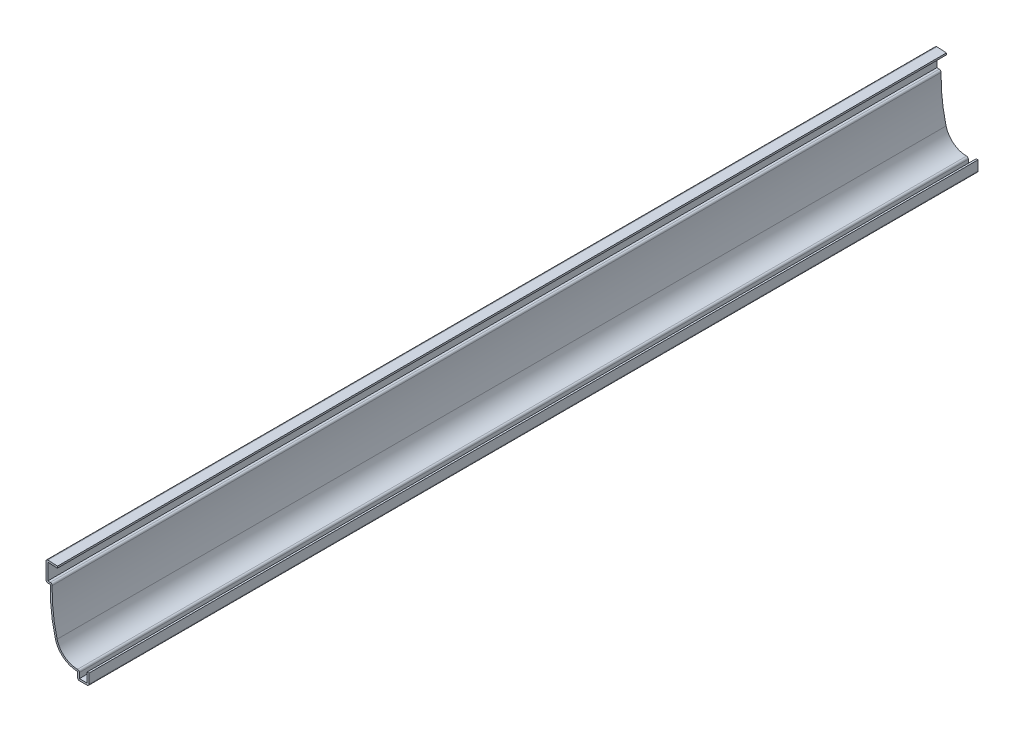
SolidWorks part; units mm, degrees
ref_plane "Front Plane" through (0, 0, 0) normal (0, 0, 1) x (1, 0, 0)
ref_plane "Top Plane" through (0, 0, 0) normal (0, 1, 0) x (1, 0, 0)
ref_plane "Right Plane" through (0, 0, 0) normal (1, 0, 0) x (0, 0, -1)
sketch "Sketch1" plane through (0, 0, 0) normal (0, 0, 1) x (1, 0, 0)
  line L0 (0, 6.35) -> (0, 0)
  line L1 (0, 0) -> (-6.35, 0)
  line L2 (-6.35, 0) -> (-6.35, 3.9687)
  line L3 (-21.4313, 38.1) -> (-23.8125, 38.1)
  line L4 (-23.8125, 38.1) -> (-23.8125, 49.2125)
  line L5 (-23.8125, 49.2125) -> (-17.4625, 48.8797)
  arc A0 (-6.35, 3.9687) -> (-18.6477, 13.4976) centre (-6.35, 16.6688) cw
  arc A1 (-18.6477, 13.4976) -> (-21.4313, 38.1) centre (67.4362, 35.6959) cw
  point P9 (49.8498, 29.128)
  point P13 (-17.7266, 28.566)
  point P14 (-21.6126, 38.1)
  dimension "D3" = 12.7
  dimension "D5" = 88.9
  dimension "D6" = 34.1313
  dimension "D12" = 2.3813
  dimension "D1" = 6.35
  dimension "D2" = 6.35
  dimension "D4" = 3.9688
  dimension "D7" = 49.2125
  dimension "D8" = 11.1125
  dimension "D9" = 6.35
  dimension "D10" = 23.8125
  dimension "D11" = 87
extrude "Extrude-Thin1" add sketch "Sketch1" against normal blind 492.125 thin
fillet "Fillet1" radius 1.016 6 edges at (0, 0, -246.0625) (-6.35, 0, -246.0625) (-5.334, 5.029, -246.0625) (-20.3812, 39.116, -246.0625) (-23.8125, 38.1, -246.0625) (-23.8125, 49.2125, -246.0625)
